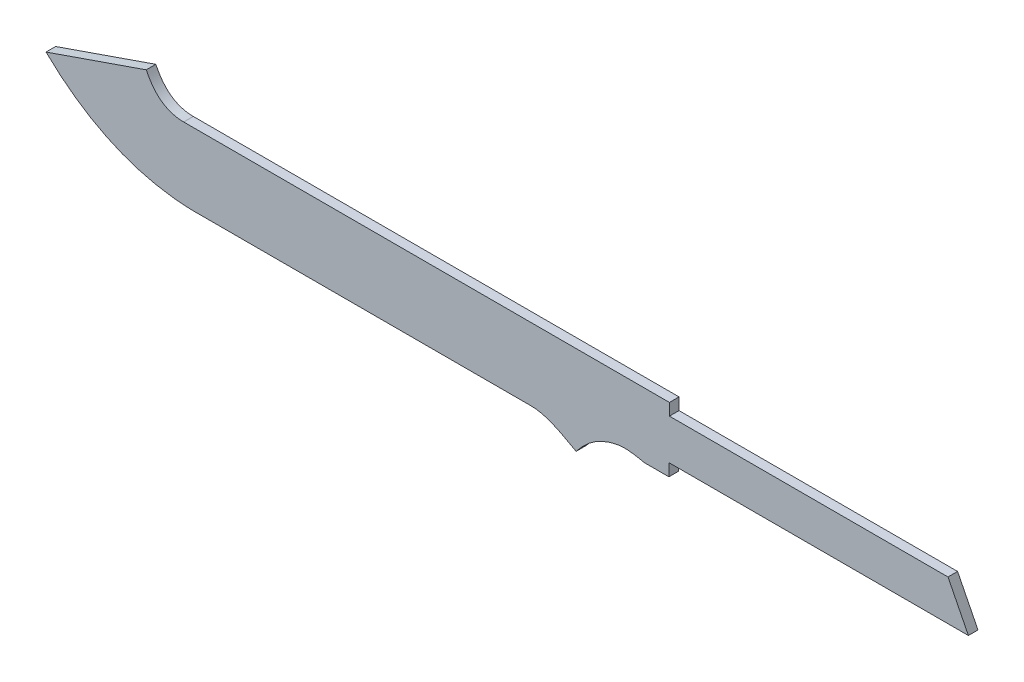
SolidWorks part; units mm, degrees
ref_plane "Ebene vorne" through (0, 0, 0) normal (0, 0, 1) x (1, 0, 0)
ref_plane "Ebene oben" through (0, 0, 0) normal (0, 1, 0) x (1, 0, 0)
ref_plane "Ebene rechts" through (0, 0, 0) normal (1, 0, 0) x (0, 0, -1)
sketch "Skizze1" plane through (0, 0, 0) normal (0, 0, 1) x (1, 0, 0)
  line L0 (831.6475, 366.4485) -> (628.5728, 366.4485)
  line L1 (628.5728, 366.4485) -> (628.5728, 375.107)
  line L2 (628.5728, 375.107) -> (274.4289, 375.107)
  line L3 (247.1226, 394.3836) -> (174.0381, 369.0851)
  line L4 (280.2516, 322.5037) -> (527.8435, 322.5037)
  line L6 (610.0387, 327.9325) -> (628.1748, 327.9325)
  line L7 (628.1748, 327.9325) -> (628.1748, 336.9111)
  line L8 (628.1748, 336.9111) -> (846.5267, 336.9111)
  line L9 (831.6475, 366.4485) -> (846.5267, 336.9111)
  spline S0 degree 2 poles (274.4289, 375.107) (256.3585, 375.107) (247.1226, 394.3836) knots 0 0 0 1 1 1
  spline S1 degree 3 poles (174.0381, 369.0851) (207.4178, 336.7093) (244.1262, 323.5559) (280.2516, 322.5037) knots 0 0 0 0 1 1 1 1
  spline S2 degree 3 poles (527.8435, 322.5037) (541.993, 322.5037) (557.3581, 311.2629) (560.6166, 310.2854) knots 0 0 0 0 1 1 1 1
  spline S3 degree 3 poles (560.6166, 310.2854) (569.0162, 321.3643) (579.4728, 327.8236) (591.9861, 329.6632) knots 0 0 0 0 1 1 1 1
  spline S4 degree 3 poles (591.9861, 329.6632) (599.5339, 330.7729) (610.0171, 327.9325) (610.0387, 327.9325) knots 0 0 0 0 1 1 1 1
extrude "Aufsatz-Linear austragen1" add sketch "Skizze1" along normal mid plane 7
